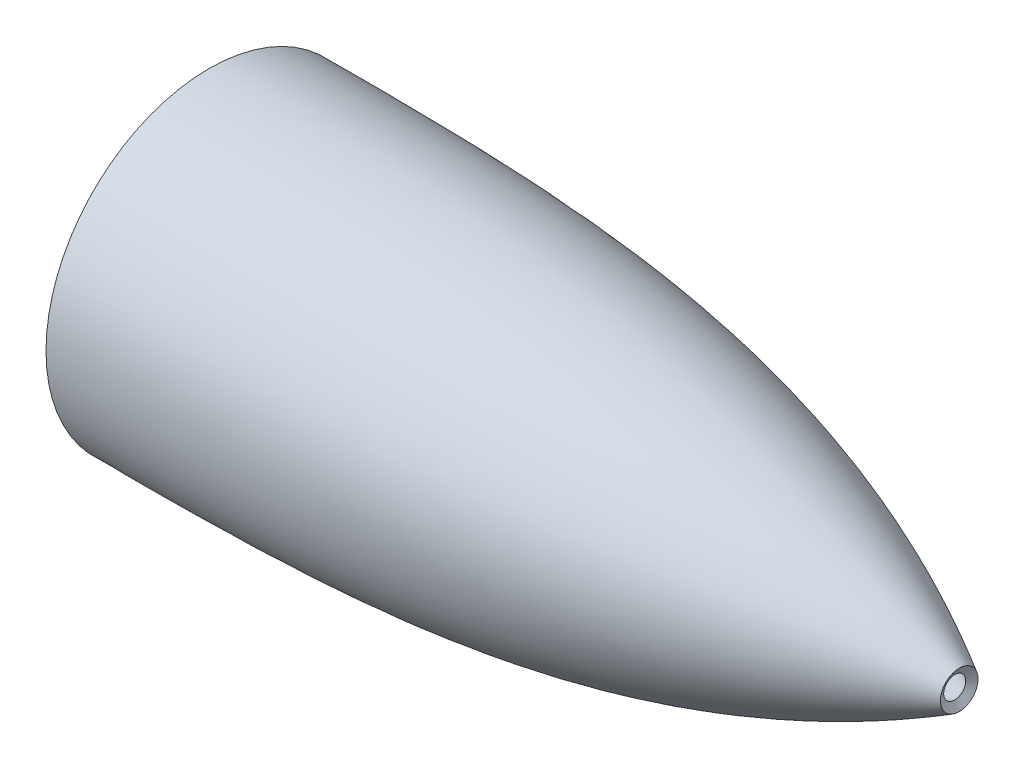
SolidWorks part; units mm, degrees
material "C (Grafite)"
ref_plane "Piano frontale" through (0, 0, 0) normal (0, 0, 1) x (1, 0, 0)
ref_plane "Piano superiore" through (0, 0, 0) normal (0, 1, 0) x (1, 0, 0)
ref_plane "Piano destro" through (0, 0, 0) normal (1, 0, 0) x (0, 0, -1)
sketch "Schizzo1" plane through (0, 0, 0) normal (0, 0, 1) x (1, 0, 0)
  line L1 (-2001.1, 6.1) -> (-1998.5998, 10.43)
  line L2 (-2414.2, 85.2885) -> (-2414.2009, 90.2885)
  spline S2 degree 3 poles (-2414.2009, 90.2885) (-2378.3995, 90.2949) (-2342.5977, 90.3174) (-2297.8933, 88.6213) (-2288.9548, 88.196) (-2271.0839, 87.1304) (-2262.1495, 86.49) (-2235.3687, 84.1835) (-2217.5949, 82.1355) (-2182.2536, 76.7233) (-2164.6862, 73.3589) (-2145.0618, 68.6876) (-2142.8829, 68.1562) (-2138.5362, 67.0701) (-2132.0303, 65.4057) (-2125.5671, 63.6339) (-2112.6987, 59.9447) (-2104.1971, 57.2908) (-2078.9314, 48.7296) (-2062.4065, 42.2211) (-2030.0122, 27.5583) (-2014.1426, 19.4046) (-1998.5998, 10.43) knots 0 0 0 0 0.25 0.25 0.3125 0.3125 0.375 0.375 0.5 0.5 0.625 0.625 0.640625 0.640625 0.65625 0.6875 0.6875 0.75 0.75 0.875 0.875 1 1 1 1
  spline S6 degree 3 poles (-2414.2, 85.2885) (-2276.5, 85.3132) (-2138.8, 85.6093) (-2001.1, 6.1) knots 0.07354 0.07354 0.07354 0.07354 0.915776 0.915776 0.915776 0.915776
sketch "Schizzo2" plane through (0, 0, 0) normal (0, 0, 1) x (1, 0, 0)
  line L0 (-2491.002, 0) -> (-1967.9126, 0)
revolve "Rivoluzione1" add sketch "Schizzo1" angle 360 about L0
